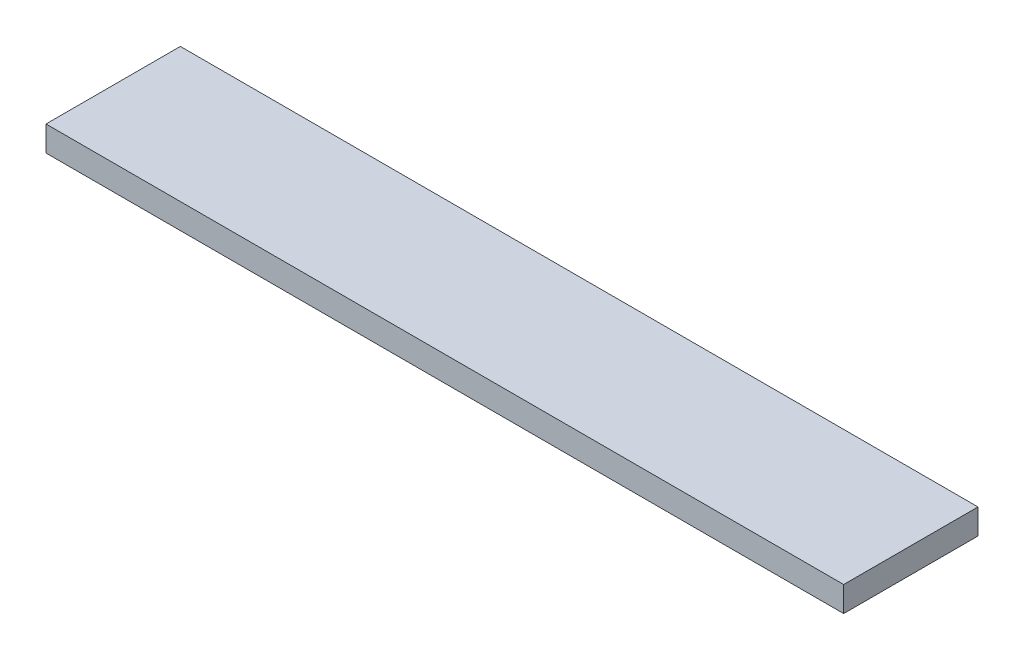
SolidWorks part; units mm, degrees
ref_plane "Alzado" through (0, 0, 0) normal (0, 0, 1) x (1, 0, 0)
ref_plane "Planta" through (0, 0, 0) normal (0, 1, 0) x (1, 0, 0)
ref_plane "Vista lateral" through (0, 0, 0) normal (1, 0, 0) x (0, 0, -1)
sketch "Croquis1" plane through (0, 0, 0) normal (0, 1, 0) x (1, 0, 0)
  line L1 (-47.5, -8) -> (47.5, -8)
  line L2 (-47.5, -8) -> (-47.5, 8)
  line L3 (-47.5, 8) -> (47.5, 8)
  line L4 (47.5, -8) -> (47.5, 8)
  line L5 (-47.5, -8) -> (47.5, 8) construction
  line L6 (-47.5, 8) -> (47.5, -8) construction
  point P0 (0, 0)
  dimension "D1" = 95
  dimension "D2" = 16
extrude "Saliente-Extruir1" add sketch "Croquis1" along normal blind 3
